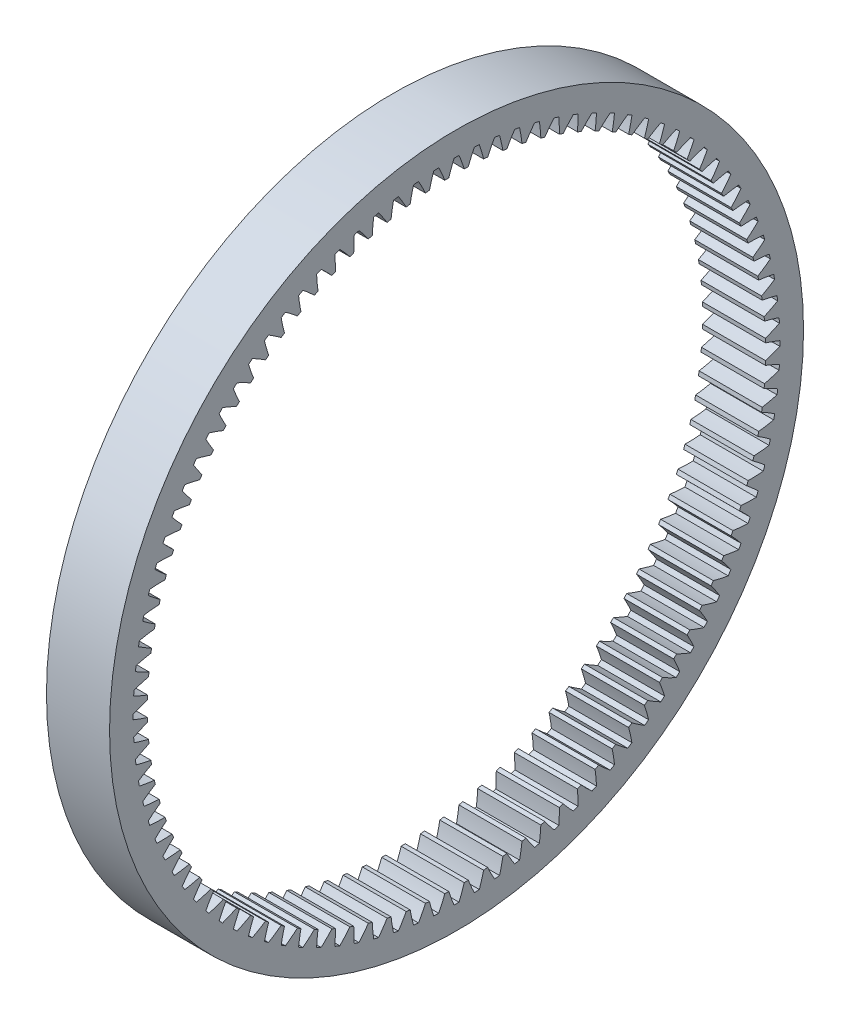
SolidWorks part; units mm, degrees
material "1.0035 (S185)"
ref_plane "Plane1" through (0, 0, 0) normal (0, 0, 1) x (1, 0, 0)
ref_plane "Plane2" through (0, 0, 0) normal (0, 1, 0) x (1, 0, 0)
ref_plane "Plane3" through (0, 0, 0) normal (1, 0, 0) x (0, 0, -1)
sketch "HoldingSke" plane through (0, 0, 0) normal (0, 1, 0) x (1, 0, 0)
  line L0 (0, 0) -> (-0.3473, -1.9696)
  line L1 (-15, 0) -> (100, 0) construction
  line L2 (0, 0) -> (-2.1039, 2.3779)
  line L3 (0, 0) -> (-11.863, 4.5341)
  line L4 (0, 0) -> (-1.4996, 8.5048)
  line L5 (0, 0) -> (-23.7986, -8.8762)
  line L6 (0, 0) -> (-10.5278, -7.1032)
  line L7 (-2.1039, 2.3779) -> (3.3635, 27.1825)
  line L8 (-76.2, 2.8779) -> (-54.61, 2.8779)
  line L9 (-71.009, 38.7566) -> (-53.1078, 45.2721)
  line L10 (-76.2, 71.12) -> (104.1128, 71.12)
  line L11 (0, 0) -> (-5, 0)
  line L12 (-76.2, 101.6) -> (-76.181, 101.6)
  line L13 (24.9733, 27.94) -> (52.9518, 28.4284)
  line L14 (24.9733, 27.94) -> (24.9743, 27.94)
  line L15 (24.9733, 27.94) -> (100.4006, 29.5858)
  circle A0 centre (0, 0) radius 27.5
  circle A1 centre (0, 0) radius 12.7
  circle A2 centre (0, 0) radius 12.7
  dimension "MHD" = 25.4
  dimension "Hub_dia" = 25.4
  dimension "Diameter" = 55
  dimension "Num_teeth" = 100
  dimension "Pitch_radius" = 180.3128
  dimension "Pitch" = 2
  dimension "Width" = 5
  dimension "Overall_len" = 25.4
  dimension "Show_teeth" = 100
  dimension "Thickness" = 12.7
  dimension "OAL" = 25.4001
  dimension "T_dim" = 21.59
  dimension "Ap" = 20
  dimension "H" = 19.05
  dimension "Backlash" = 0.019
  dimension "Addendum_fac" = 1
  dimension "Dedendum_fac" = 1.25
  dimension "Clearance_fac" = 0.25
  dimension "Dedendum_add" = 0.001
  dimension "Module" = 0.5
sketch "BasProSke" plane through (0, 0, 0) normal (0, 1, 0) x (1, 0, 0)
  line L0 (-10, 0) -> (60, 0) construction
  line L1 (0, 24.5) -> (0, 27.5)
  line L2 (0, 24.5) -> (5, 24.5)
  line L3 (5, 24.5) -> (5, 27.5)
  line L4 (5, 27.5) -> (0, 27.5)
  dimension "Diameter" = 55
  dimension "Thickness" = 5
  dimension "Inside_diameter" = 49
revolve "Base-Revolve" add sketch "BasProSke" angle 360 about L0
sketch "TooCutSke" plane through (0, 0, 0) normal (1, 0, 0) x (0, 0, -1)
  line L3 (0.4402, 24.9961) -> (0.4402, 53.6633) construction
  line L4 (0, 0) -> (0, 59.563) construction
  line L5 (0, 0) -> (-2.1462, 68.2938) construction
  line L6 (-11.3335, 20.7974) -> (37.16, 22.3213) construction
  circle A0 centre (0, 0) radius 25 construction
  circle A1 centre (0, 0) radius 25.626 construction
  circle A2 centre (0, 0) radius 21.1431 construction
  circle A3 centre (0, 0) radius 24.4746 construction
  arc A4 (0.6157, 24.4669) -> (0.1965, 25.6252) centre (-11.3335, 20.7974) ccw
  arc A5 (0.6157, 24.4669) -> (-0.6157, 24.4669) centre (0, 0) ccw
  arc A6 (0.1965, 25.6252) -> (-0.1965, 25.6252) centre (0, 0) ccw
  arc A7 (-0.1965, 25.6252) -> (-0.6157, 24.4669) centre (11.3335, 20.7974) ccw
  dimension "Pitch_dia" = 50
  dimension "Base_dia" = 42.2862
  dimension "Root_dia" = 51.252
  dimension "Overcut_dia" = 48.9492
  dimension "Flank_rad" = 12.5
  dimension "Half_ang" = 1.8
  dimension "Half_CT" = 0.4402
extrude "ToothCut" cut sketch "TooCutSke" along normal through all
fillet "Breaks" [suppressed] radius 0.05
fillet "RootFillets" [suppressed] radius 0.126
pattern_circular "TeethCuts" count 100 every 3.6 about axis through (-10, 0, 0) along (1, 0, 0) of "RootFillets", "Breaks", "ToothCut"
equation "' \"Module@HoldingSke\" = 6.35"
equation "' \"Num_teeth@HoldingSke\" = 24"
equation "' \"Ap@HoldingSke\" =  14.5"
equation "' \"Width@HoldingSke\" = 12"
equation "' \"Diameter@HoldingSke\" = 8 * 25.4"
equation "' \"Show_teeth@HoldingSke\" = 100"
equation "' \"Backlash@HoldingSke\" = 0.009 * 25.4"
equation "' \"Addendum_fac@HoldingSke\" = 1.0"
equation "' \"Dedendum_fac@HoldingSke\" = 1.25"
equation "' \"Dedendum_add@HoldingSke\" = 0.00005 * 25.4"
equation "' \"Clearance_fac@HoldingSke\" = 0.25"
equation "\"Pitch@HoldingSke\" = 1 / \"Module@HoldingSke\" "
equation "\"Overcut_dia@TooCutSke\" = (\"Num_teeth@HoldingSke\" - 2 * \"Addendum_fac@HoldingSke\") / \"Pitch@HoldingSke\" - 0.002 * 25.4"
equation "\"Pitch_dia@TooCutSke\" = \"Num_teeth@HoldingSke\" / \"Pitch@HoldingSke\""
equation "\"Base_dia@TooCutSke\" = \"Num_teeth@HoldingSke\" / \"Pitch@HoldingSke\" * cos((\"Ap@HoldingSke\"  * 3.14159265 / 180)) * 0.90"
equation "\"Root_dia@TooCutSke\" = \"Num_teeth@HoldingSke\"  / \"Pitch@HoldingSke\" + 2 *  \"Dedendum_fac@HoldingSke\"/ \"Pitch@HoldingSke\" + \"Dedendum_add@HoldingSke\" * 2"
equation "\"Half_ang@TooCutSke\" = 180 / \"Num_teeth@HoldingSke\""
equation "\"Half_CT@TooCutSke\" = \"Num_teeth@HoldingSke\" / \"Pitch@HoldingSke\" * sin((3.14159265 / 2 / \"Num_teeth@HoldingSke\")) / 2 + 10 * \"Backlash@HoldingSke\" / 4"
equation "\"Flank_rad@TooCutSke\" = \"Num_teeth@HoldingSke\" / \"Pitch@HoldingSke\" / 4"
equation "\"Radius@RootFillets\"= \"Clearance_fac@HoldingSke\" / \"Pitch@HoldingSke\" + \"Dedendum_add@HoldingSke\""
equation "\"Break_rad@Breaks\" = 0.02 / \"Pitch@HoldingSke\" * 5"
equation "\"Num_teeth@TeethCuts\" = int( \"Show_teeth@HoldingSke\" ) + 1"
equation "\"Num_teeth@TeethCuts\" = ((sgn( \"Num_teeth@TeethCuts\" - \"Num_teeth@HoldingSke\" )-1)*( \"Num_teeth@TeethCuts\" - \"Num_teeth@HoldingSke\" ))/-2+ \"Num_teeth@HoldingSke\""
equation "\"Num_teeth@TeethCuts\" = ((sgn( \"Num_teeth@TeethCuts\" - 2.0)+1)*( \"Num_teeth@TeethCuts\" - 2.0))/2 +2.0"
equation "\"Angle@TeethCuts\" = 360.0 / \"Num_teeth@HoldingSke\""
equation "\"Diameter@BasProSke\" = \"Num_teeth@HoldingSke\"  / \"Pitch@HoldingSke\" + 2 *  \"Dedendum_fac@HoldingSke\"/ \"Pitch@HoldingSke\" + \"Dedendum_add@HoldingSke\" * 2 + 0.002 * 25.4"
equation "\"Diameter@BasProSke\" = ((sgn( \"Diameter@BasProSke\"  - \"Diameter@HoldingSke\" )+1)*( \"Diameter@BasProSke\"  - \"Diameter@HoldingSke\" ))/2 + \"Diameter@HoldingSke\""
equation "\"Inside_diameter@BasProSke\" =  (\"Num_teeth@HoldingSke\" - 2 * \"Addendum_fac@HoldingSke\") / \"Pitch@HoldingSke\" "
equation "\"Thickness@BasProSke\"  = \"Width@HoldingSke\""
